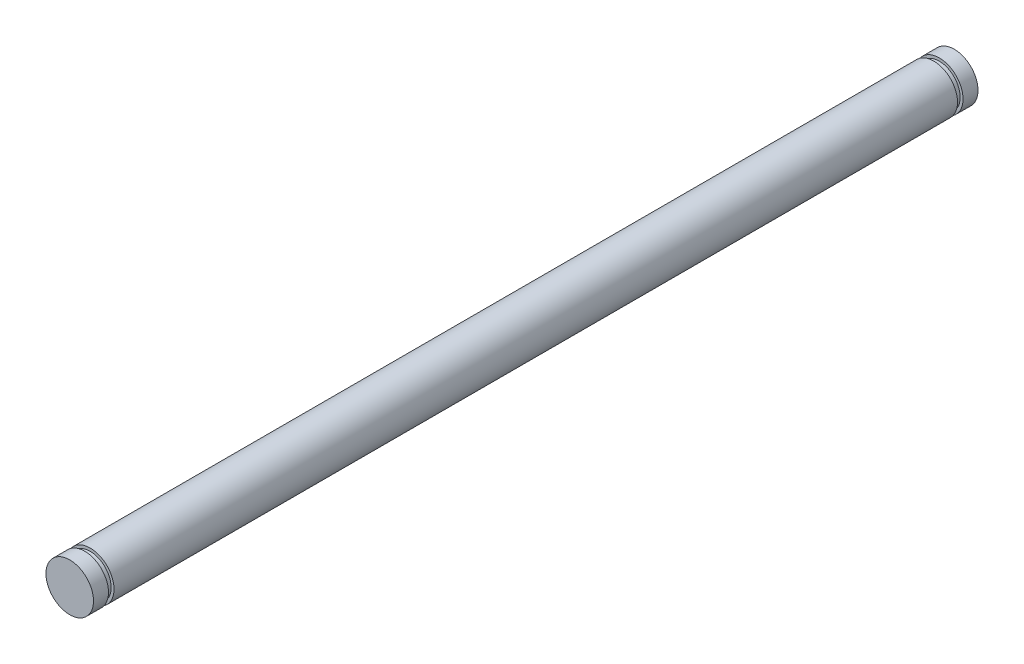
SolidWorks part; units mm, degrees
ref_plane "Front" through (0, 0, 0) normal (0, 0, 1) x (1, 0, 0)
ref_plane "Top" through (0, 0, 0) normal (0, 1, 0) x (1, 0, 0)
ref_plane "Right" through (0, 0, 0) normal (1, 0, 0) x (0, 0, -1)
sketch "Sketch2" plane through (0, 0, 0) normal (0, 0, 1) x (1, 0, 0)
  circle A0 centre (0, 0) radius 3.175
  dimension "D1" = 6.35
extrude "Boss-Extrude1" add sketch "Sketch2" along normal blind 56.32
sketch "Sketch3" plane through (0, 0, 56.32) normal (0, 0, 1) x (1, 0, 0)
  circle A0 centre (0, 0) radius 2.794
  dimension "D1" = 5.588
extrude "Boss-Extrude2" add sketch "Sketch3" along normal blind 0.7366
sketch "Sketch4" plane through (0, 0, 57.0566) normal (0, 0, 1) x (1, 0, 0)
  circle A0 centre (0, 0) radius 3.175
  dimension "D1" = 6.35
extrude "Boss-Extrude3" add sketch "Sketch4" along normal blind 2
mirror "Mirror1" about plane through (0, 0, 0) normal (0, 0, 1) of "Boss-Extrude2", "Boss-Extrude1", "Boss-Extrude3"
